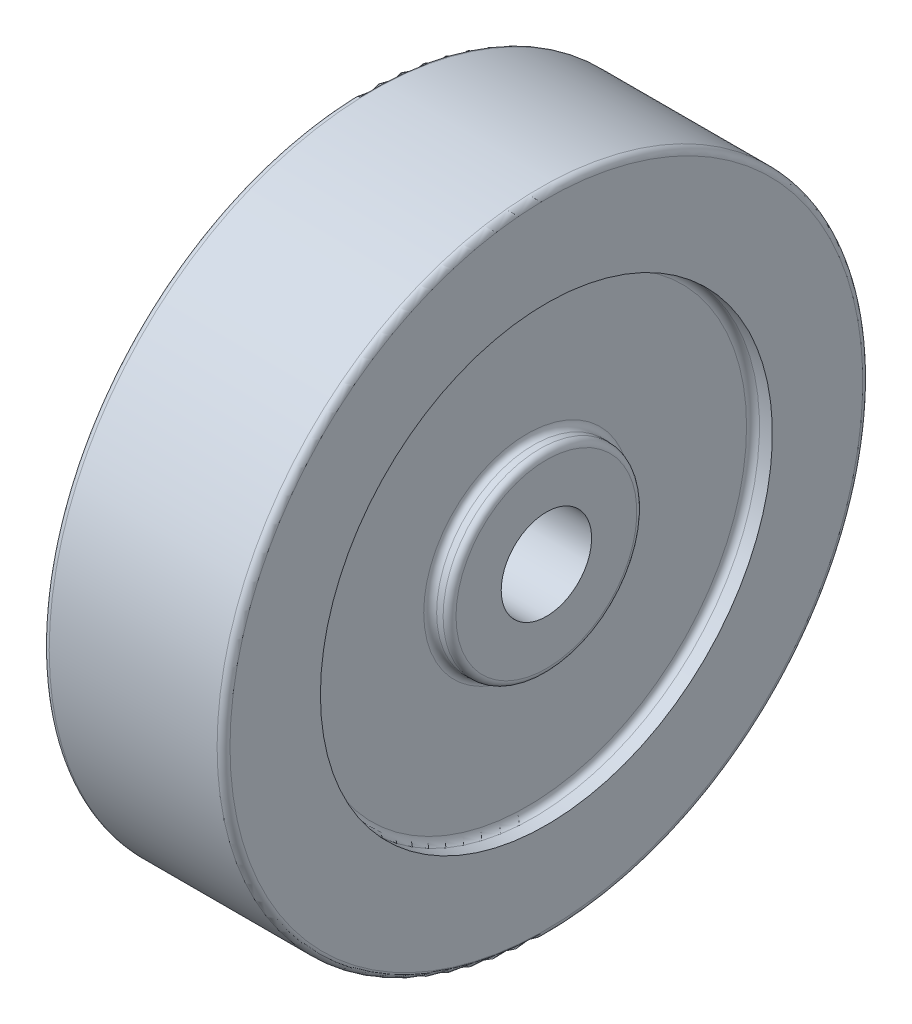
SolidWorks part; units mm, degrees
ref_plane "Front Plane" through (0, 0, 0) normal (0, 0, 1) x (1, 0, 0)
ref_plane "Top Plane" through (0, 0, 0) normal (0, 1, 0) x (1, 0, 0)
ref_plane "Right Plane" through (0, 0, 0) normal (1, 0, 0) x (0, 0, -1)
sketch "Sketch1" plane through (0, 0, 0) normal (0, 0, 1) x (1, 0, 0)
  line L0 (0, 0) -> (56.1842, 0) construction
  line L1 (-14, 7) -> (14, 7)
  line L2 (14, 7) -> (14, 15)
  line L3 (14, 15) -> (11, 15)
  line L4 (11, 15) -> (11, 35)
  line L5 (11, 35) -> (14, 35)
  line L6 (14, 35) -> (14, 50)
  line L7 (14, 50) -> (-14, 50)
  line L8 (-14, 50) -> (-14, 35)
  line L9 (-14, 35) -> (-11, 35)
  line L10 (-11, 35) -> (-11, 15)
  line L11 (-11, 15) -> (-14, 15)
  line L12 (-14, 15) -> (-14, 7)
  line L13 (0, 0) -> (0, 30.585) construction
  point P15 (0, 7)
  dimension "D1" = 7
  dimension "D2" = 15
  dimension "D3" = 35
  dimension "D4" = 50
  dimension "D5" = 28
  dimension "D6" = 3
revolve "Revolve1" add sketch "Sketch1" angle 360 about L0
fillet "Fillet1" radius 1 8 edges at (11, 0, 35) (11, 0, 15) (14, 0, 15) (-11, 0, 15) (-14, 0, 15) (-11, 0, 35) (14, 0, 50) (-14, 0, 50)
